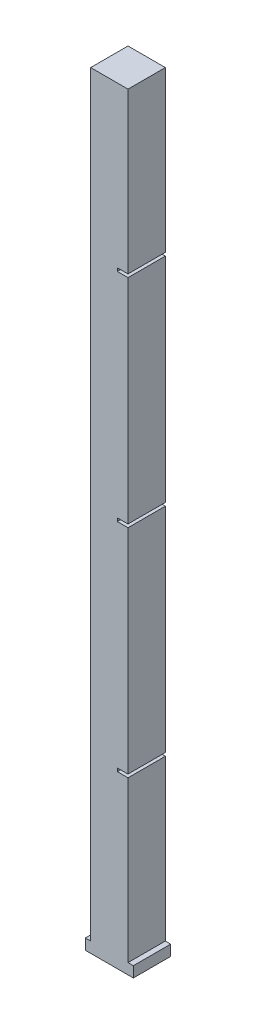
SolidWorks part; units mm, degrees
ref_plane "Front Plane" through (0, 0, 0) normal (0, 0, 1) x (1, 0, 0)
ref_plane "Top Plane" through (0, 0, 0) normal (0, 1, 0) x (1, 0, 0)
ref_plane "Right Plane" through (0, 0, 0) normal (1, 0, 0) x (0, 0, -1)
sketch "Sketch2" plane through (0, 0, 0) normal (0, 0, 1) x (1, 0, 0)
  line L0 (0, 0) -> (90, 0)
  line L1 (90, 0) -> (90, 20)
  line L2 (0, 0) -> (0, 20)
  line L3 (90, 20) -> (80, 20)
  line L4 (0, 20) -> (10, 20)
  line L5 (80, 20) -> (80, 320)
  line L6 (80, 320) -> (60, 320)
  line L7 (60, 320) -> (60, 326)
  line L8 (60, 326) -> (80, 326)
  line L9 (80, 326) -> (80, 726)
  line L10 (80, 726) -> (60, 726)
  line L11 (60, 726) -> (60, 732)
  line L12 (60, 732) -> (80, 732)
  line L13 (80, 732) -> (80, 1132)
  line L14 (80, 1132) -> (60, 1132)
  line L15 (60, 1132) -> (60, 1138)
  line L16 (60, 1138) -> (80, 1138)
  line L17 (80, 1138) -> (80, 1438)
  line L18 (80, 1438) -> (10, 1438)
  line L19 (10, 1438) -> (10, 20)
  dimension "D1" = 90
  dimension "D2" = 20
  dimension "D3" = 20
  dimension "D4" = 10
  dimension "D5" = 10
  dimension "D6" = 300
  dimension "D7" = 6
  dimension "D8" = 400
  dimension "D9" = 20
  dimension "D10" = 20
  dimension "D11" = 20
  dimension "D12" = 6
  dimension "D13" = 20
  dimension "D14" = 400
  dimension "D15" = 20
  dimension "D16" = 6
  dimension "D17" = 20
  dimension "D18" = 300
  dimension "D19" = 70
extrude "Boss-Extrude1" add sketch "Sketch2" along normal blind 70
